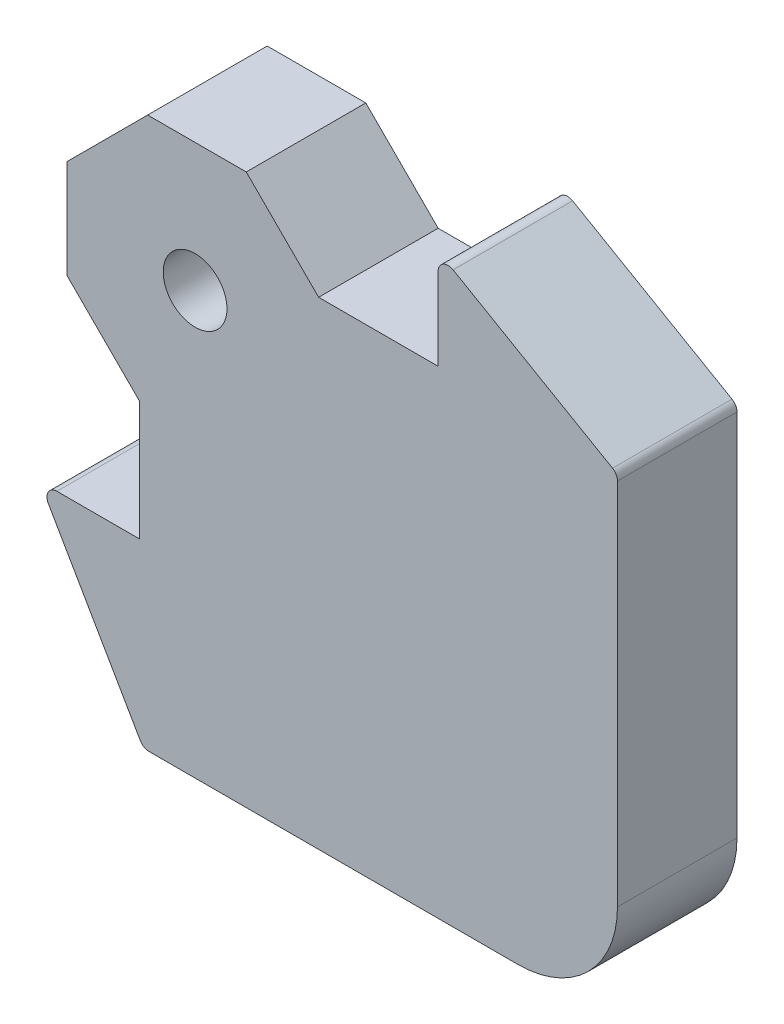
SolidWorks part; units mm, degrees
material "Acrylic (Medium-high impact)"
ref_plane "Front Plane" through (0, 0, 0) normal (0, 0, 1) x (1, 0, 0)
ref_plane "Top Plane" through (0, 0, 0) normal (0, 1, 0) x (1, 0, 0)
ref_plane "Right Plane" through (0, 0, 0) normal (1, 0, 0) x (0, 0, -1)
sketch "Sketch1" plane through (0, 0, 0) normal (0, 0, 1) x (1, 0, 0)
  line L0 (0, 0) -> (-21.2132, 0)
  line L2 (-21.2132, 0) -> (0, 21.2132)
  line L4 (0, 21.2132) -> (0, 0)
  line L5 (-10.6066, 10.6066) -> (-6.2, 6.2) construction
  line L6 (-6.2, 6.2) -> (0, 0) construction
  circle A0 centre (-6.2, 6.2) radius 1.6
  dimension "D3" = 3.2
  dimension "D2" = 15
  dimension "D4" = 6.2
extrude "Boss-Extrude1" add sketch "Sketch1" along normal mid plane 6
sketch "Sketch2" plane through (0, 0, 0) normal (0, 0, 1) x (1, 0, 0)
  line L0 (-9, 0) -> (-9, -6)
  line L1 (-21.2132, 0) -> (0, 0) construction
  line L2 (-9, -6) -> (-14, -6)
  line L3 (-14, -6) -> (-8.8038, -15)
  line L4 (-8.8038, -15) -> (10, -15)
  line L5 (-9, 0) -> (0, 0)
  line L6 (0, 0) -> (0, 9)
  line L7 (0, 0) -> (0, 21.2132) construction
  line L8 (0, 9) -> (6, 9)
  line L9 (6, 9) -> (6, 14)
  line L10 (6, 14) -> (15, 8.8038)
  line L11 (15, 8.8038) -> (15, -10)
  line L12 (0, 0) -> (15, -15) construction
  arc A0 (15, -10) -> (10, -15) centre (10, -10) cw
  dimension "D5" = 5
  dimension "D1" = 6
  dimension "D2" = 9
  dimension "D3" = 5
  dimension "D4" = 9
  dimension "D6" = 60
extrude "Boss-Extrude2" add sketch "Sketch2" along normal mid plane 6
fillet "Fillet1" radius 0.5 4 edges at (-14, -6, 0) (6, 14, 0) (-8.8038, -15, 0) (15, 8.8038, 0)
sketch "Sketch4" plane through (0, 0, 3) normal (0, 0, 1) x (1, 0, 0)
  line L0 (0, 9) -> (-6.1066, 15.1066)
  line L1 (0, 9) -> (0, 21.2132) construction
  line L2 (6, 9) -> (0, 9) construction
  line L3 (0, 21.2132) -> (-21.2132, 0) construction
  line L4 (-6.1066, 15.1066) -> (0, 21.2132)
  line L5 (0, 21.2132) -> (0, 9)
  line L6 (-21.2132, 0) -> (-15.1066, 6.1066)
  line L7 (-15.1066, 6.1066) -> (-9, 0)
  line L8 (-9, 0) -> (-21.2132, 0)
extrude "Cut-Extrude1" cut sketch "Sketch4" against normal up to next
chamfer "Chamfer1" distance 3.5 angle 45 2 edges at (-15.1066, 6.1066, 0) (-6.1066, 15.1066, 0)
